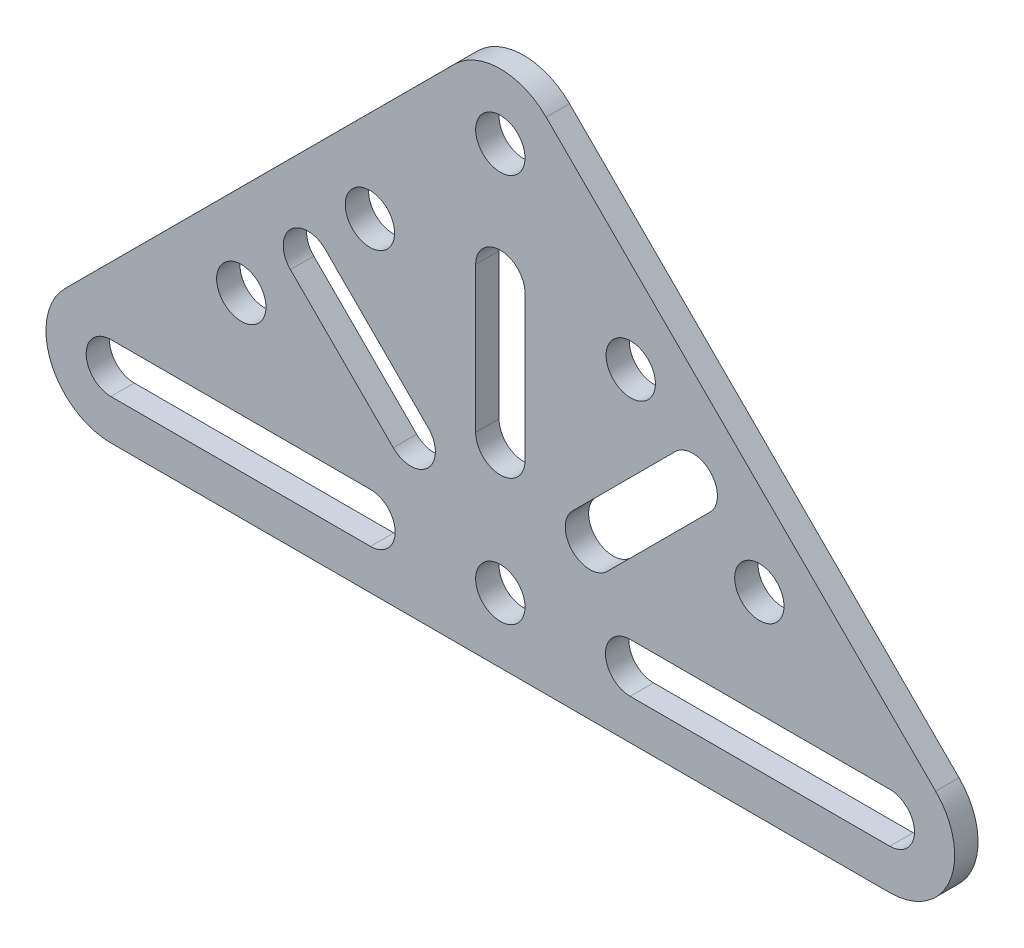
SolidWorks part; units mm, degrees
material "1060 Alloy"
ref_plane "Front Plane" through (0, 0, 0) normal (0, 0, 1) x (1, 0, 0)
ref_plane "Top Plane" through (0, 0, 0) normal (0, 1, 0) x (1, 0, 0)
ref_plane "Right Plane" through (0, 0, 0) normal (1, 0, 0) x (0, 0, -1)
other "Center of Mass"
sketch "Sketch1" plane through (0, 0, 0) normal (0, 0, 1) x (1, 0, 0)
  line L0 (0, 0) -> (0, 38.0526) construction
  line L1 (38.1, 0) -> (-38.1, 0) construction
  line L2 (-38.1, 0) -> (0, 38.0526) construction
  line L3 (38.1, 0) -> (0, 38.0526) construction
  line L4 (0, 0) -> (-19.0381, 19.0381) construction
  line L5 (0, 0) -> (19.0381, 19.0381) construction
  line L6 (-42.5873, 4.4929) -> (-4.4873, 42.5455)
  line L7 (42.5873, 4.4929) -> (4.4873, 42.5455)
  line L8 (38.1, -6.35) -> (-38.1, -6.35)
  line L9 (53.4438, -6.35) -> (0, 47.0272) construction
  line L10 (53.4438, -6.35) -> (-53.4438, -6.35) construction
  line L11 (-53.4438, -6.35) -> (0, 47.0272) construction
  arc A0 (42.5873, 4.4929) -> (38.1, -6.35) centre (38.1, 0) cw
  arc A1 (-4.4873, 42.5455) -> (4.4873, 42.5455) centre (0, 38.0526) cw
  arc A2 (-42.5873, 4.4929) -> (-38.1, -6.35) centre (-38.1, 0) ccw
  dimension "D5" = 6.35
  dimension "D1" = 45
  dimension "D2" = 76.2
  dimension "D3" = 53.848
  dimension "D4" = 6.35
extrude "Boss-Extrude1" add sketch "Sketch1" along normal blind 2.286
sketch "Sketch2" plane through (0, 0, 2.286) normal (0, 0, 1) x (1, 0, 0)
  line L0 (0, 38.0526) -> (0, 0) construction
  line L1 (-38.1, 0) -> (0, 38.0526) construction
  circle A0 centre (0, 0) radius 2.413
  circle A1 centre (0, 38.0526) radius 2.413
  circle A2 centre (-25.3401, 12.744) radius 2.413
  circle A3 centre (25.3401, 12.744) radius 2.413
  circle A4 centre (-12.7599, 25.3085) radius 2.413
  circle A5 centre (12.7599, 25.3085) radius 2.413
  dimension "D1" = 4.826
  dimension "D2" = 18.034
  dimension "D3" = 35.814
extrude "Cut-Extrude1" cut sketch "Sketch2" against normal through all
sketch "Sketch3" plane through (0, 0, 2.286) normal (0, 0, 1) x (1, 0, 0)
  line L1 (-38.1, 2.413) -> (-12.7, 2.413)
  line L3 (-38.1, -2.413) -> (-12.7, -2.413)
  arc A0 (-12.7, 2.413) -> (-12.7, -2.413) centre (-12.7, 0) cw
  arc A1 (-38.1, 2.413) -> (-38.1, -2.413) centre (-38.1, 0) ccw
  circle A2 centre (0, 0) radius 2.413 construction
  dimension "D1" = 25.4
extrude "Cut-Extrude2" cut sketch "Sketch3" against normal through all
mirror "Mirror1" about plane through (0, 0, 0) normal (1, 0, 0) of "Cut-Extrude2"
sketch "Sketch4" plane through (0, 0, 2.286) normal (0, 0, 1) x (1, 0, 0)
  line L0 (-18.8251, 18.8251) -> (-8.7672, 8.7672) construction
  line L1 (0, 0) -> (-19.0381, 19.0381) construction
  line L2 (-17.1188, 20.5313) -> (-7.0609, 10.4734)
  line L3 (-20.5313, 17.1188) -> (-10.4734, 7.0609)
  arc A0 (-17.1188, 20.5313) -> (-20.5313, 17.1188) centre (-18.8251, 18.8251) ccw
  arc A1 (-10.4734, 7.0609) -> (-7.0609, 10.4734) centre (-8.7672, 8.7672) ccw
  circle A2 centre (0, 0) radius 2.413 construction
  point P4 (-13.7961, 13.7961)
  dimension "D1" = 14.224
extrude "Cut-Extrude3" cut sketch "Sketch4" against normal through all
pattern_circular "CirPattern1" count 3 over 90 about axis through (0, 0, 0) along (0, 0, 1) of "Cut-Extrude3"
